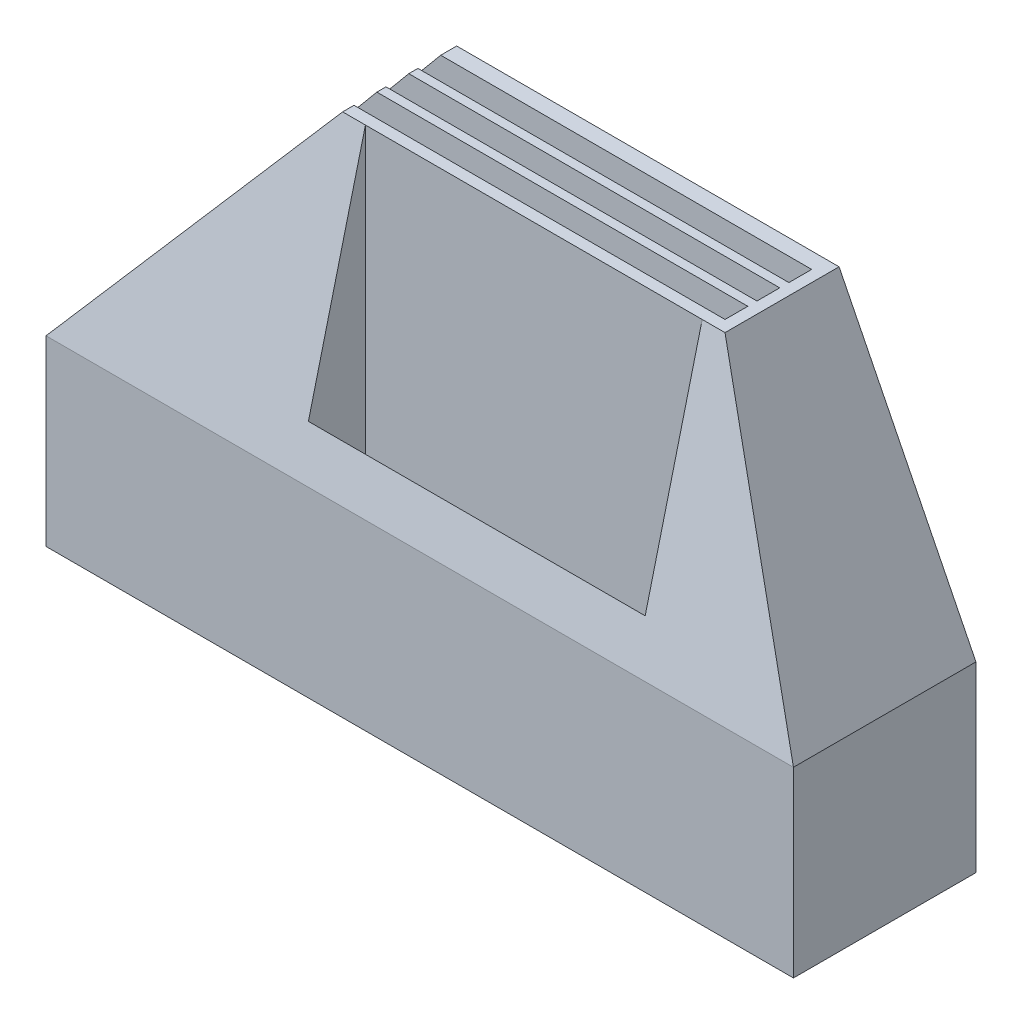
SolidWorks part; units mm, degrees
material "Custom Plastic"
ref_plane "Front Plane" through (0, 0, 0) normal (0, 0, 1) x (1, 0, 0)
ref_plane "Top Plane" through (0, 0, 0) normal (0, 1, 0) x (1, 0, 0)
ref_plane "Right Plane" through (0, 0, 0) normal (1, 0, 0) x (0, 0, -1)
sketch "Sketch1" plane through (0, 0, 0) normal (0, 1, 0) x (1, 0, 0)
  line L1 (0, 0) -> (416.08, 0)
  line L2 (0, 0) -> (0, 101.6)
  line L3 (0, 101.6) -> (416.08, 101.6)
  line L4 (416.08, 0) -> (416.08, 101.6)
extrude "Boss-Extrude2" add sketch "Sketch1" along normal blind 254
sketch "Sketch2" plane through (0, 0, 0) normal (0, 0, 1) x (1, 0, 0)
  line L0 (0, 101.6) -> (0, 254)
  line L1 (0, 254) -> (0, 0) construction
  line L2 (0, 254) -> (127, 254)
  line L3 (0, 254) -> (416.08, 254) construction
  line L4 (127, 254) -> (0, 101.6)
  line L5 (416.08, 254) -> (416.08, 101.6)
  line L6 (416.08, 254) -> (416.08, 0) construction
  line L7 (416.08, 101.6) -> (339.88, 254)
  line L8 (339.88, 254) -> (416.08, 254)
  dimension "D1" = 152.4
  dimension "D2" = 127
  dimension "D3" = 76.2
extrude "Cut-Extrude1" cut sketch "Sketch2" against normal blind 101.6
sketch "Sketch6" plane through (0, 0, 0) normal (0, 1, 0) x (1, 0, 0)
  line L0 (127, 101.6) -> (127, 0) construction
  line L1 (139.7, 38.1) -> (327.18, 38.1)
  line L2 (139.7, 38.1) -> (139.7, 6.35)
  line L3 (139.7, 6.35) -> (327.18, 6.35)
  line L4 (327.18, 38.1) -> (327.18, 6.35)
  line L5 (139.7, 38.1) -> (327.18, 6.35) construction
  line L6 (139.7, 6.35) -> (327.18, 38.1) construction
  line L7 (416.08, 0) -> (416.08, 101.6) construction
  line L13 (127, 0) -> (339.88, 0) construction
  dimension "D1" = 31.75
  dimension "D2" = 6.35
  dimension "D3" = 12.7
  dimension "D4" = 88.9
extrude "Cut-Extrude9" cut sketch "Sketch6" along normal through all from offset 10.16
sketch "Sketch8" plane through (0, 254, 0) normal (0, 1, 0) x (1, 0, 0)
  line L0 (416.08, 0) -> (416.08, 101.6) construction
  line L1 (6.35, 44.45) -> (333.53, 44.45)
  line L2 (6.35, 44.45) -> (6.35, 57.15)
  line L3 (6.35, 57.15) -> (333.53, 57.15)
  line L4 (333.53, 44.45) -> (333.53, 57.15)
  line L5 (6.35, 44.45) -> (333.53, 57.15) construction
  line L6 (6.35, 57.15) -> (333.53, 44.45) construction
  line L7 (0, 101.6) -> (0, 0) construction
  line L9 (6.35, 62.23) -> (6.35, 74.93)
  line L10 (6.35, 62.23) -> (333.53, 62.23)
  line L11 (333.53, 62.23) -> (333.53, 74.93)
  line L12 (6.35, 74.93) -> (333.53, 74.93)
  line L13 (6.35, 80.01) -> (6.35, 92.71)
  line L14 (6.35, 80.01) -> (333.53, 80.01)
  line L15 (333.53, 80.01) -> (333.53, 92.71)
  line L16 (6.35, 92.71) -> (333.53, 92.71)
  line L17 (327.18, 38.1) -> (139.7, 38.1) construction
  point P0 (169.94, 50.8)
  dimension "D1" = 82.55
  dimension "D2" = 6.35
  dimension "D3" = 6.35
  dimension "D4" = 12.7
  dimension "D5" = 3
extrude "Cut-Extrude11" cut sketch "Sketch8" against normal blind 228.6
sketch "Sketch9" plane through (416.08, 0, 0) normal (1, 0, 0) x (0, 0, -1)
  line L0 (0, 254) -> (0, 101.6)
  line L1 (0, 101.6) -> (38.1, 254)
  line L2 (44.45, 254) -> (0, 254) construction
  line L3 (38.1, 254) -> (0, 254)
  dimension "D1" = 38.1
extrude "Cut-Extrude12" cut sketch "Sketch9" against normal through all
sketch "Sketch10" plane through (0, 0, -38.1) normal (0, 0, 1) x (1, 0, 0)
  line L0 (327.18, 254) -> (327.18, 127) construction
  line L1 (314.48, 10.4541) -> (152.4, 10.4541)
  line L2 (314.48, 10.4541) -> (314.48, 23.6587)
  line L3 (314.48, 23.6587) -> (152.4, 23.6587)
  line L4 (152.4, 10.4541) -> (152.4, 23.6587)
  line L5 (139.7, 127) -> (139.7, 254) construction
  dimension "D1" = 12.7
  dimension "D2" = 12.7
extrude "Cut-Extrude13" cut sketch "Sketch10" against normal up to next
